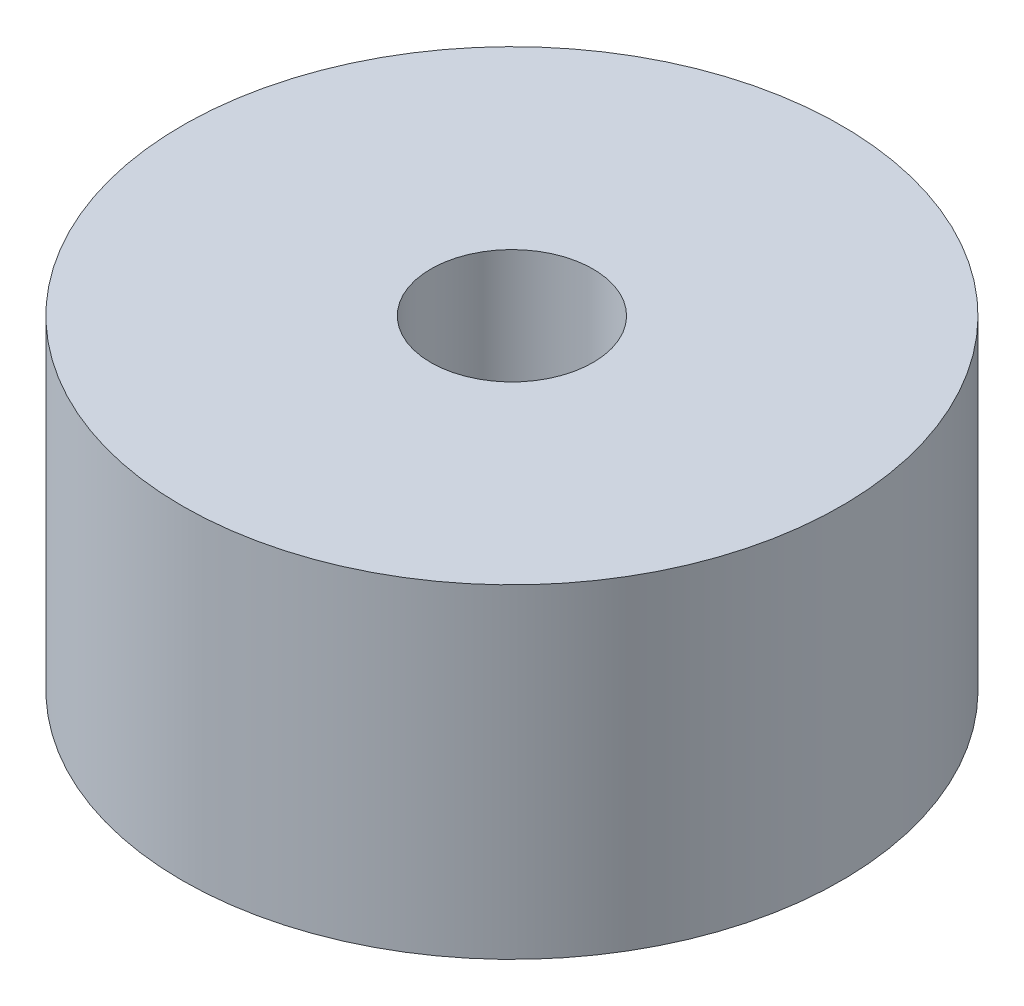
SolidWorks part; units mm, degrees
ref_plane "Front" through (0, 0, 0) normal (0, 0, 1) x (1, 0, 0)
ref_plane "Top" through (0, 0, 0) normal (0, 1, 0) x (1, 0, 0)
ref_plane "Right" through (0, 0, 0) normal (1, 0, 0) x (0, 0, -1)
sketch "Sketch1" plane through (0, 0, 0) normal (0, 1, 0) x (1, 0, 0)
  circle A0 centre (0, 0) radius 6.35 construction
  circle A1 centre (0, 0) radius 1.6891 construction
  circle A2 centre (0, 0) radius 6.4516
  circle A3 centre (0, 0) radius 1.5875
  dimension "D1" = 12.7
  dimension "D2" = 3.3782
  dimension "D3" = 0.1016
  dimension "D4" = 0.1016
extrude "Boss-Extrude1" add sketch "Sketch1" along normal blind 6.35
